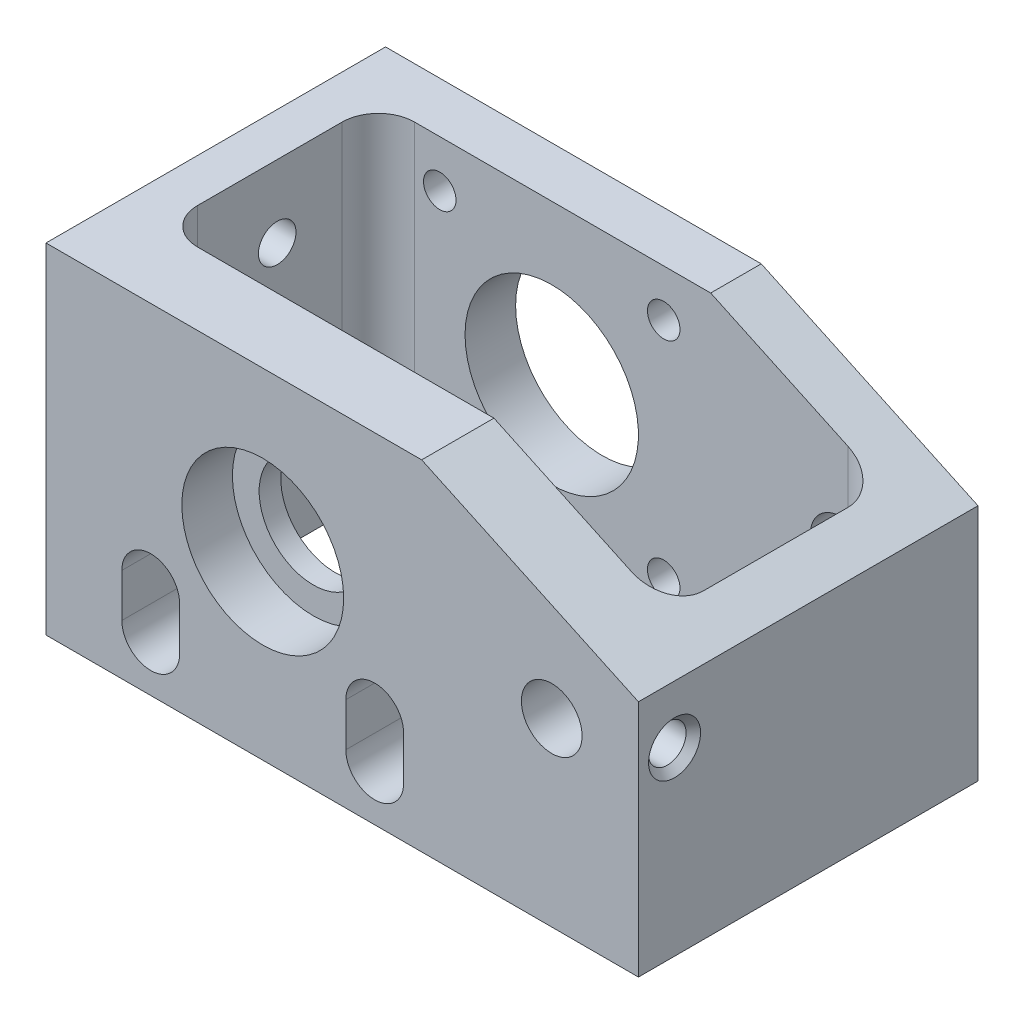
SolidWorks part; units mm, degrees
ref_plane "Front Plane" through (0, 0, 0) normal (0, 0, 1) x (1, 0, 0)
ref_plane "Top Plane" through (0, 0, 0) normal (0, 1, 0) x (1, 0, 0)
ref_plane "Right Plane" through (0, 0, 0) normal (1, 0, 0) x (0, 0, -1)
sketch "Sketch1" plane through (0, 0, 0) normal (0, 0, 1) x (1, 0, 0)
  line L0 (-30, -25) -> (-30, 22)
  line L1 (-30, 22) -> (22, 22)
  line L2 (22, 22) -> (52, 8)
  line L3 (52, 8) -> (52, -25)
  line L4 (52, -25) -> (-30, -25)
  circle A0 centre (0, 0) radius 7.5
  circle A1 centre (40, 0) radius 4.2
  dimension "D1" = 15
  dimension "D6" = 8.4
  dimension "D2" = 40
  dimension "D3" = 30
  dimension "D4" = 25
  dimension "D5" = 22
  dimension "D7" = 12
  dimension "D8" = 33
  dimension "D9" = 22
extrude "Boss-Extrude1" add sketch "Sketch1" along normal blind 47
sketch "Sketch2" plane through (0, 0, 47) normal (0, 0, 1) x (1, 0, 0)
  circle A0 centre (0, 0) radius 11.2
  dimension "D1" = 22.4
extrude "Cut-Extrude1" cut sketch "Sketch2" against normal blind 7
sketch "Sketch3" plane through (0, 0, 0) normal (0, 0, -1) x (-1, 0, 0)
  line L0 (-15.5, 15.5) -> (15.5, -15.5) construction
  circle A0 centre (-15.5, 15.5) radius 2.25
  circle A1 centre (-15.5, -15.5) radius 2.25
  circle A2 centre (15.5, -15.5) radius 2.25
  circle A3 centre (15.5, 15.5) radius 2.25
  circle A4 centre (0, 0) radius 12
  dimension "D1" = 4.5
  dimension "D4" = 24
  dimension "D2" = 31
  dimension "D3" = 31
extrude "Cut-Extrude2" cut sketch "Sketch3" against normal blind 15
sketch "Sketch4" plane through (0, 22, 0) normal (0, 1, 0) x (1, 0, 0)
  line L0 (22, 0) -> (-30, 0) construction
  line L1 (-19, -7) -> (41, -7)
  line L2 (-24, -12) -> (-24, -32)
  line L3 (-19, -37) -> (41, -37)
  line L4 (46, -12) -> (46, -32)
  line L5 (22, -47) -> (-30, -47) construction
  line L6 (-30, -47) -> (-30, 0) construction
  line L7 (52, -47) -> (52, 0) construction
  arc A0 (41, -37) -> (46, -32) centre (41, -32) ccw
  arc A1 (41, -7) -> (46, -12) centre (41, -12) cw
  arc A2 (-19, -7) -> (-24, -12) centre (-19, -12) ccw
  arc A3 (-24, -32) -> (-19, -37) centre (-19, -32) ccw
  dimension "D5" = 5
  dimension "D1" = 7
  dimension "D2" = 10
  dimension "D3" = 6
  dimension "D4" = 6
extrude "Cut-Extrude3" cut sketch "Sketch4" against normal through all
sketch "Sketch6" plane through (0, 0, 47) normal (0, 0, 1) x (1, 0, 0)
  line L0 (-30, -25) -> (52, -25) construction
  line L2 (-19.5, -12) -> (-19.5, -18)
  line L3 (-11.5, -12) -> (-11.5, -18)
  line L4 (11.5, -12) -> (11.5, -18)
  line L5 (19.5, -12) -> (19.5, -18)
  arc A0 (-11.5, -12) -> (-19.5, -12) centre (-15.5, -12) ccw
  arc A1 (19.5, -12) -> (11.5, -12) centre (15.5, -12) ccw
  arc A3 (-19.5, -18) -> (-11.5, -18) centre (-15.5, -18) ccw
  arc A4 (11.5, -18) -> (19.5, -18) centre (15.5, -18) ccw
  dimension "D1" = 8
  dimension "D2" = 15.5
  dimension "D3" = 13
  dimension "D4" = 15.5
  dimension "D5" = 7
extrude "Cut-Extrude4" cut sketch "Sketch6" against normal blind 20
sketch "Sketch7" plane through (52, 0, 0) normal (1, 0, 0) x (0, 0, -1)
  line L0 (-47, -25) -> (-47, 8) construction
  circle A0 centre (-42, 0) radius 2.6
  dimension "D1" = 5.2
  dimension "D2" = 5
extrude "Cut-Extrude5" cut sketch "Sketch7" against normal blind 10
sketch "Sketch8" plane through (0, -25, 0) normal (0, -1, 0) x (1, 0, 0)
  line L0 (-30, 47) -> (52, 47) construction
  line L1 (-30, 47) -> (-30, 0) construction
  line L2 (-30, 0) -> (52, 0) construction
  line L3 (52, 47) -> (52, 0) construction
  circle A0 centre (-25, 42) radius 2.6
  circle A1 centre (-25, 5) radius 2.6
  circle A2 centre (47, 5) radius 2.6
  circle A3 centre (47, 42) radius 2.6
  dimension "D1" = 5.2
  dimension "D2" = 5
  dimension "D3" = 5
  dimension "D4" = 5
  dimension "D5" = 5
extrude "Cut-Extrude6" cut sketch "Sketch8" against normal blind 8
chamfer "Chamfer1" distance 1 angle 45 4 edges at (49.6, -25, 42) (49.6, -25, 5) (-22.4, -25, 5) (-22.4, -25, 42)
sketch "Sketch9" plane through (-30, 0, 0) normal (-1, 0, 0) x (0, 0, 1)
  line L0 (0, 22) -> (0, -25) construction
  line L1 (47, 22) -> (0, 22) construction
  line L2 (47, 22) -> (47, -25) construction
  circle A0 centre (41, 12) radius 2.6
  circle A1 centre (21, 12) radius 2.6
  dimension "D4" = 5.2
  dimension "D1" = 21
  dimension "D2" = 10
  dimension "D3" = 6
extrude "Cut-Extrude7" cut sketch "Sketch9" against normal blind 10
chamfer "Chamfer2" distance 1 angle 45 1 edges at (52, 2.6, 42)
